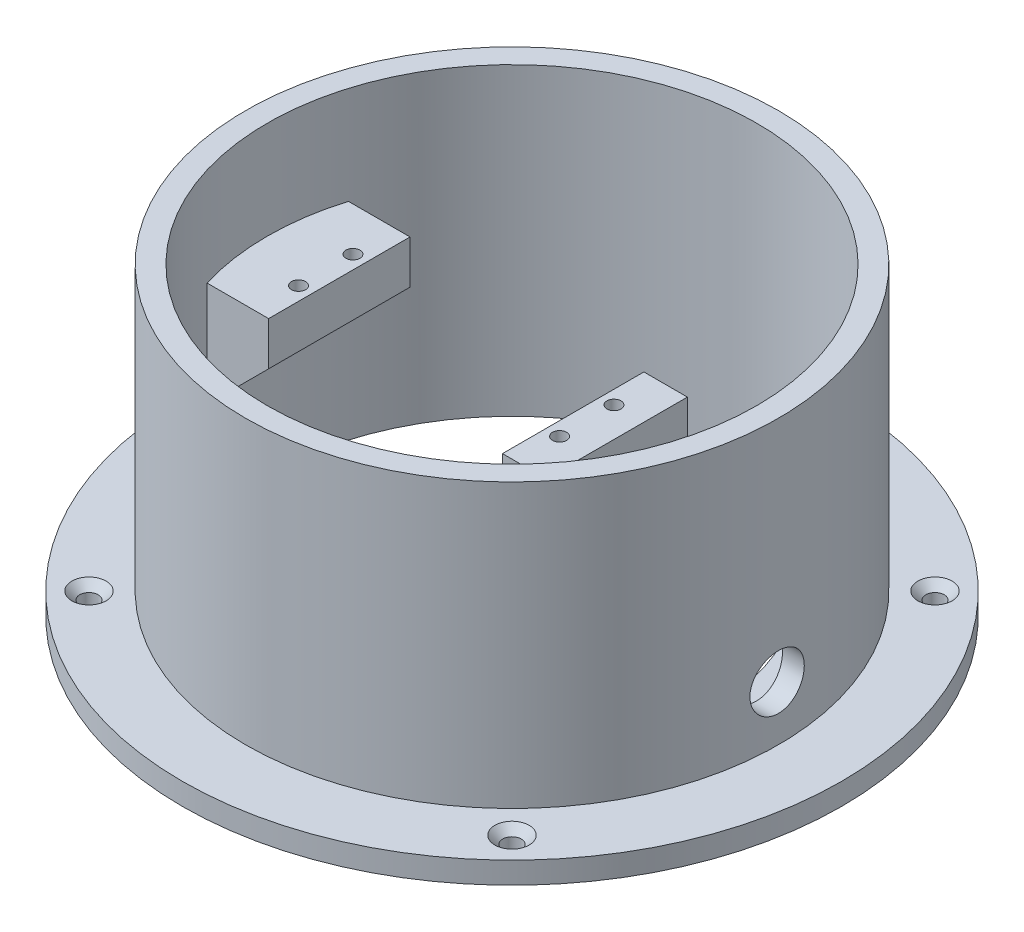
SolidWorks part; units mm, degrees
ref_plane "Front Plane" through (0, 0, 0) normal (0, 0, 1) x (1, 0, 0)
ref_plane "Top Plane" through (0, 0, 0) normal (0, 1, 0) x (1, 0, 0)
ref_plane "Right Plane" through (0, 0, 0) normal (1, 0, 0) x (0, 0, -1)
sketch "Sketch1" plane through (0, 0, 0) normal (0, 1, 0) x (1, 0, 0)
  circle A0 centre (0, 0) radius 60.625
  circle A1 centre (0, 0) radius 45
  dimension "D1" = 121.25
  dimension "D2" = 90
extrude "Boss-Extrude1" add sketch "Sketch1" along normal blind 4 contours A0
sketch "Sketch2" plane through (0, 4, 0) normal (0, 1, 0) x (1, 0, 0)
  circle A0 centre (0, 0) radius 45 construction
  circle A1 centre (0, 0) radius 45
  circle A2 centre (0, 0) radius 49
  dimension "D1" = 4
extrude "Boss-Extrude2" add sketch "Sketch2" along normal blind 52
ref_plane "Plane1" through (0, 36, 0) normal (0, 1, 0) x (1, 0, 0)
sketch "Sketch4" plane through (0, 0, 0) normal (0, 0, 1) x (1, 0, 0)
  line L0 (-60.625, 0) -> (60.625, 0) construction
  line L1 (11.25, 38) -> (19.25, 38)
  line L2 (11.25, 38) -> (11.25, 0)
  line L3 (11.25, 0) -> (19.25, 0)
  line L4 (19.25, 38) -> (19.25, 0)
  line L5 (49, 56) -> (-49, 56) construction
  line L6 (-45, 56) -> (-45, 4)
  line L7 (-31.75, 38) -> (-46.75, 38)
  line L8 (-31.75, 38) -> (-31.75, 30)
  line L9 (-31.75, 30) -> (-46.75, 30)
  line L10 (-46.75, 38) -> (-46.75, 30)
  line L11 (60.625, 4) -> (-60.625, 4) construction
  line L12 (-31.75, 30) -> (-45, 16.75)
  dimension "D1" = 11.25
  dimension "D2" = 8
  dimension "D3" = 18
  dimension "D4" = 43
  dimension "D5" = 15
  dimension "D6" = 8
  dimension "D7" = 45
  dimension "D8" = 18
extrude "Boss-Extrude4" add sketch "Sketch4" along normal mid plane 26 contours L9 L8 L7 L6 | L12 L9 L6 | L1 L4 L3 L2
sketch "Sketch5" plane through (0, 0, 0) normal (0, -1, 0) x (1, 0, 0)
  line L0 (11.25, 13) -> (29.0674, 34.3524)
  line L1 (11.25, -13) -> (29.0674, -34.3524)
  line L2 (11.25, 13) -> (11.25, -13)
  circle A0 centre (0, 0) radius 45 construction
  arc A1 (29.0674, -34.3524) -> (29.0674, 34.3524) centre (0, 0) ccw
extrude "Boss-Extrude5" add sketch "Sketch5" against normal up to surface (4 mm away) contours L0 A1 L1 L2 up to face at (0, 4, 60.625)
sketch "Sketch7" plane through (0, 38, 0) normal (0, 1, 0) x (1, 0, 0)
  line L0 (-31.75, -13) -> (-31.75, 13) construction
  circle A0 centre (-34.25, 5) radius 1.3
  circle A1 centre (-34.25, -5) radius 1.3
  circle A2 centre (13.75, 5) radius 1.3
  circle A3 centre (13.75, -5) radius 1.3
  dimension "D1" = 2.6
  dimension "D2" = 2.6
  dimension "D3" = 10
  dimension "D4" = 5
  dimension "D5" = 2.5
  dimension "D7" = 48
  dimension "D6" = 2
extrude "Cut-Extrude4" cut sketch "Sketch7" against normal blind 7.2
sketch "Sketch9" plane through (11.25, 0, 0) normal (-1, 0, 0) x (0, 0, 1)
  line L0 (13, 0) -> (-13, 0) construction
  line L1 (-5, 29) -> (5, 29)
  line L2 (-5, 29) -> (-5, 0)
  line L3 (-5, 0) -> (5, 0)
  line L4 (5, 29) -> (5, 0)
  line L5 (-5, 29) -> (5, 0) construction
  line L6 (-5, 0) -> (5, 29) construction
  line L7 (0, 0) -> (0, 29) construction
  line L8 (13, 38) -> (-13, 38) construction
  line L10 (5, 5) -> (-5, 5)
  point P0 (0, 14.5)
  dimension "D1" = 10
  dimension "D2" = 9
  dimension "D3" = 5
extrude "Cut-Extrude7" cut sketch "Sketch9" against normal up to surface (8 mm away) contours L10 L4 L1 L2 up to face at (19.25, 21, 0)
ref_plane "Plane2" through (49, 0, 0) normal (1, 0, 0) x (0, 0, -1)
sketch "Sketch11" plane through (49, 0, 0) normal (1, 0, 0) x (0, 0, -1)
  circle A0 centre (0, 14) radius 5
  dimension "D1" = 10
  dimension "D2" = 14
extrude "Cut-Extrude8" cut sketch "Sketch11" against normal up to next
sketch "Sketch12" plane through (0, 4, 0) normal (0, 1, 0) x (1, 0, 0)
  line L5 (27.25, 19.6878) -> (27.25, -19.6878)
  line L6 (27.25, 19.6878) -> (27.25, -19.6878)
  line L9 (24.25, 16.0926) -> (24.25, -16.0926)
  line L10 (19.25, -13) -> (19.25, 13) construction
  line L18 (27.25, -19.6878) -> (29.4795, -22.3597)
  line L19 (29.4795, 22.3597) -> (27.25, 19.6878)
  line L21 (24.25, -16.0926) -> (29.4795, -22.3597)
  line L22 (29.4795, 22.3597) -> (24.25, 16.0926)
  arc A2 (29.4795, -22.3597) -> (29.4795, 22.3597) centre (0, 0) ccw
  arc A3 (29.4795, -22.3597) -> (29.4795, 22.3597) centre (0, 0) ccw
  dimension "D2" = 5
  dimension "D1" = 8
extrude "Cut-Extrude9" cut sketch "Sketch12" against normal through all contours L21 A3 L22 L6 | L6 L22 L9 L21
sketch "Sketch14" plane through (0, 4, 0) normal (0, 1, 0) x (1, 0, 0)
  line L0 (0, 0) -> (-38.8909, 38.8909) construction
  line L1 (11.25, 13) -> (19.25, 13) construction
  circle A0 centre (-38.8909, 38.8909) radius 1.5
  circle A1 centre (38.8909, 38.8909) radius 1.5
  circle A2 centre (38.8909, -38.8909) radius 1.5
  circle A3 centre (-38.8909, -38.8909) radius 1.5
  point P15 (0, 0)
  dimension "D1" = 3
  dimension "D2" = 55
  dimension "D3" = 135
  dimension "D4" = 4
hole_wizard "CSK for M3 Countersunk Flat Head Screw1" positions "Sketch15" profile "Sketch17" countersink size "M3" standard "DIN" end condition up to next
sketch "Sketch15" plane through (0, 4, 0) normal (0, 1, 0) x (1, 0, 0)
  point P0 (-38.8909, 38.8909)
  point P3 (-38.8909, -38.8909)
  point P6 (38.8909, -38.8909)
  point P9 (38.8909, 38.8909)
sketch "Sketch17" plane through (-38.8909, 4, -38.8909) normal (1, 0, 0) x (0, 0, 1)
  line L0 (0, 0) -> (0, 4)
  line L1 (0, 4) -> (1.7, 4)
  line L2 (1.7, 4) -> (1.7, 1.45)
  line L3 (1.7, 1.45) -> (3.15, 0)
  line L5 (3.15, 0) -> (0, 0)
  line L6 (-1.7, 1.45) -> (-3.15, 0) construction
  line L11 (0, -6.35) -> (0, 107.95) construction
  dimension "Thru Hole Dia." = 3.4
  dimension "Thru Hole Depth" = 4
  dimension "Near C'Sink Dia." = 6.3
  dimension "Near C'Sink Angle" = 90
